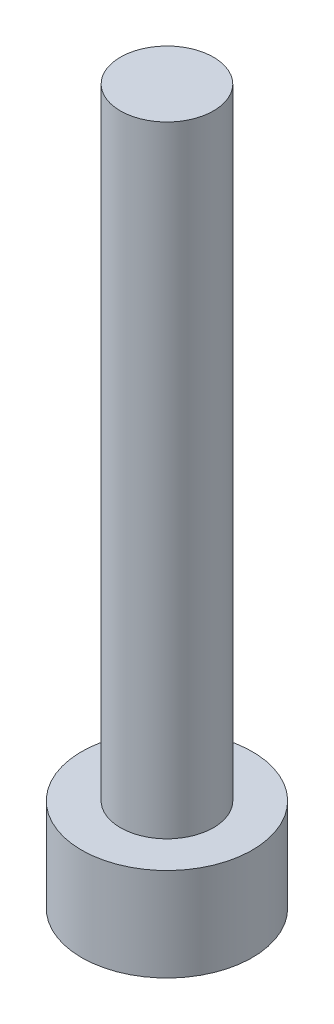
SolidWorks part; units mm, degrees
ref_plane "Front Plane" through (0, 0, 0) normal (0, 0, 1) x (1, 0, 0)
ref_plane "Top Plane" through (0, 0, 0) normal (0, 1, 0) x (1, 0, 0)
ref_plane "Right Plane" through (0, 0, 0) normal (1, 0, 0) x (0, 0, -1)
sketch "Sketch1" plane through (0, 0, 0) normal (0, 1, 0) x (1, 0, 0)
  circle A0 centre (0, 0) radius 2.75
  dimension "D1" = 5.5
extrude "Boss-Extrude1" add sketch "Sketch1" along normal blind 3
sketch "Sketch2" plane through (0, 3, 0) normal (0, 1, 0) x (1, 0, 0)
  circle A0 centre (0, 0) radius 1.5
  dimension "D1" = 3
extrude "Boss-Extrude2" add sketch "Sketch2" along normal blind 20
sketch "Sketch3" plane through (0, 0, 0) normal (0, -1, 0) x (-1, 0, 0)
  line L1 (0, -1.4434) -> (1.25, -0.7217)
  line L2 (1.25, -0.7217) -> (1.25, 0.7217)
  line L3 (1.25, 0.7217) -> (0, 1.4434)
  line L4 (0, 1.4434) -> (-1.25, 0.7217)
  line L5 (-1.25, 0.7217) -> (-1.25, -0.7217)
  line L6 (-1.25, -0.7217) -> (0, -1.4434)
  circle A0 centre (0, 0) radius 1.25 construction
  dimension "D1" = 2.5
extrude "Cut-Extrude1" cut sketch "Sketch3" against normal blind 1.5
